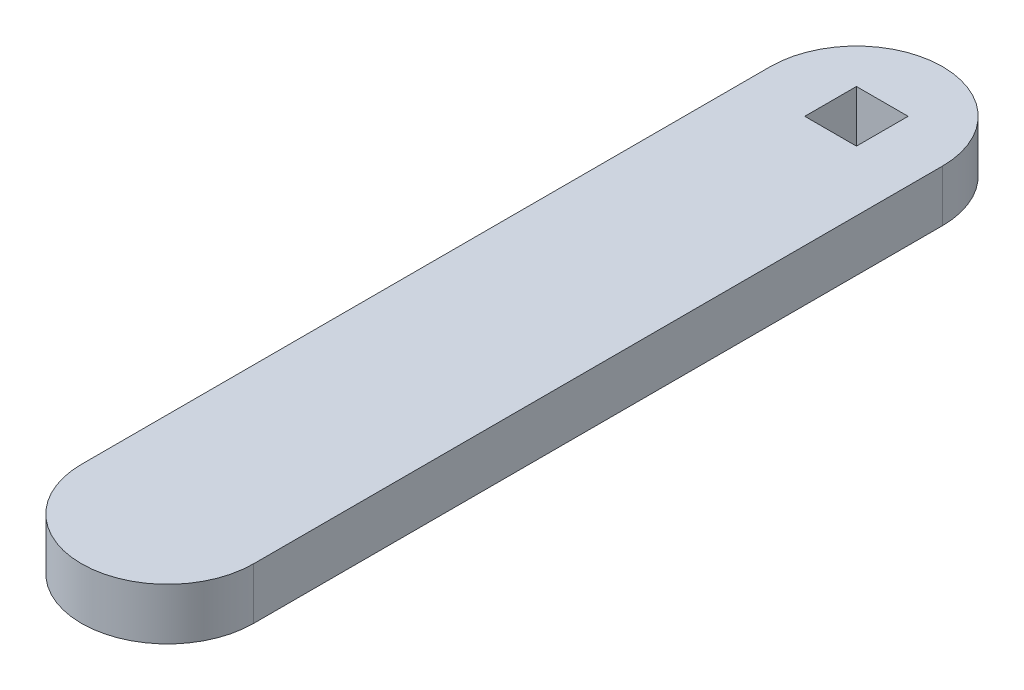
SolidWorks part; units mm, degrees
ref_plane "前视基准面" through (0, 0, 0) normal (0, 0, 1) x (1, 0, 0)
ref_plane "上视基准面" through (0, 0, 0) normal (0, 1, 0) x (1, 0, 0)
ref_plane "右视基准面" through (0, 0, 0) normal (1, 0, 0) x (0, 0, -1)
sketch "草图1" plane through (0, 0, 0) normal (0, 1, 0) x (1, 0, 0)
  line L0 (0, 200) -> (0, -200) construction
  line L1 (50, 200) -> (50, -200)
  line L2 (-50, 200) -> (-50, -200)
  arc A0 (50, 200) -> (-50, 200) centre (0, 200) ccw
  arc A1 (-50, -200) -> (50, -200) centre (0, -200) ccw
  point P2 (0, 0)
  dimension "D1" = 400
  dimension "D2" = 100
extrude "凸台-拉伸1" add sketch "草图1" along normal blind 30
sketch "草图2" plane through (0, 30, 0) normal (0, 1, 0) x (1, 0, 0)
  line L1 (-15, 185) -> (15, 185)
  line L2 (-15, 185) -> (-15, 215)
  line L3 (-15, 215) -> (15, 215)
  line L4 (15, 185) -> (15, 215)
  line L5 (-15, 185) -> (15, 215) construction
  line L6 (-15, 215) -> (15, 185) construction
  point P0 (0, 200)
  dimension "D1" = 30
  dimension "D2" = 30
extrude "切除-拉伸1" cut sketch "草图2" against normal through all
